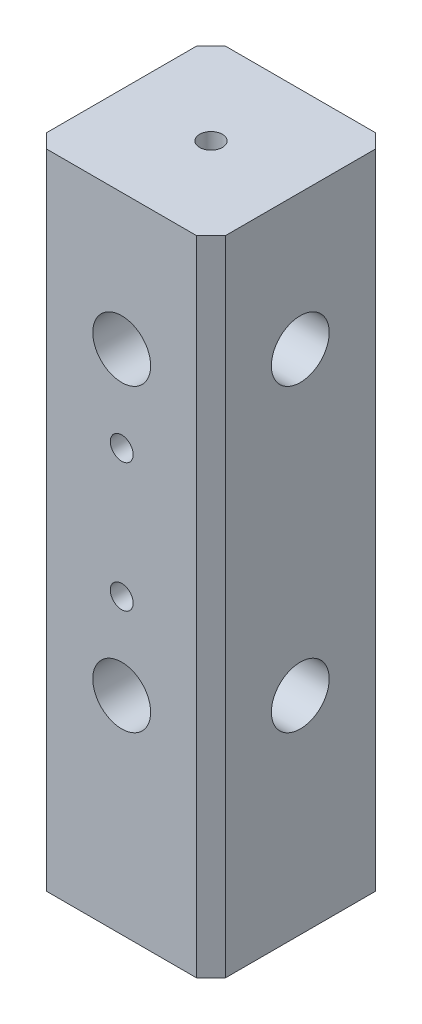
SolidWorks part; units mm, degrees
ref_plane "Front Plane" through (0, 0, 0) normal (0, 0, 1) x (1, 0, 0)
ref_plane "Top Plane" through (0, 0, 0) normal (0, 1, 0) x (1, 0, 0)
ref_plane "Right Plane" through (0, 0, 0) normal (1, 0, 0) x (0, 0, -1)
sketch "Sketch1" plane through (0, 0, 0) normal (0, 1, 0) x (1, 0, 0)
  line L1 (12.5, 12.5) -> (-12.5, 12.5)
  line L2 (12.5, 12.5) -> (12.5, -12.5)
  line L3 (12.5, -12.5) -> (-12.5, -12.5)
  line L4 (-12.5, 12.5) -> (-12.5, -12.5)
  point P4 (0, 12.5)
  point P6 (12.5, 0)
  dimension "D1" = 25
  dimension "D2" = 25
extrude "Boss-Extrude1" add sketch "Sketch1" along normal blind 90
sketch "Sketch2" plane through (12.5, 0, 0) normal (1, 0, 0) x (0, 0, -1)
  line L0 (-12.5, 90) -> (12.5, 90) construction
  line L3 (12.5, 90) -> (12.5, 0) construction
  circle A0 centre (0, 71) radius 4.05
  circle A1 centre (0, 29) radius 4.05
  dimension "D1" = 12.5
  dimension "D3" = 42
  dimension "D4" = 19
  dimension "D5" = 12.5
extrude "Cut-Extrude1" cut sketch "Sketch2" against normal blind 8 contours A1 | A0
sketch "Sketch3" plane through (0, 0, 12.5) normal (0, 0, 1) x (1, 0, 0)
  line L0 (-12.5, 90) -> (12.5, 90) construction
  line L2 (12.5, 90) -> (12.5, 0) construction
  circle A0 centre (0, 29) radius 4.05
  circle A1 centre (0, 71) radius 4.05
  dimension "D1" = 19
  dimension "D2" = 42
  dimension "D3" = 12.5
  dimension "D4" = 12.5
extrude "Cut-Extrude7" cut sketch "Sketch3" against normal blind 8 contours A0 | A1
chamfer "Chamfer1" distance 2 angle 45 1 edges at (12.5, 45, 12.5)
sketch "Sketch4" plane through (0, 90, 0) normal (0, 1, 0) x (1, 0, 0)
sketch "Sketch5" plane through (0, 0, 12.5) normal (0, 0, 1) x (1, 0, 0)
  circle A0 centre (0, 59) radius 1.6
  circle A1 centre (0, 41) radius 1.6
  circle A2 centre (0, 71) radius 4.05 construction
  circle A3 centre (0, 29) radius 4.05 construction
  dimension "D1" = 12
  dimension "D2" = 12
extrude "Cut-Extrude8" cut sketch "Sketch5" against normal blind 12.5
sketch "Sketch6" plane through (0, 90, 0) normal (0, 1, 0) x (1, 0, 0)
  circle A0 centre (0, 0) radius 1.6
extrude "Cut-Extrude9" cut sketch "Sketch6" against normal blind 10
